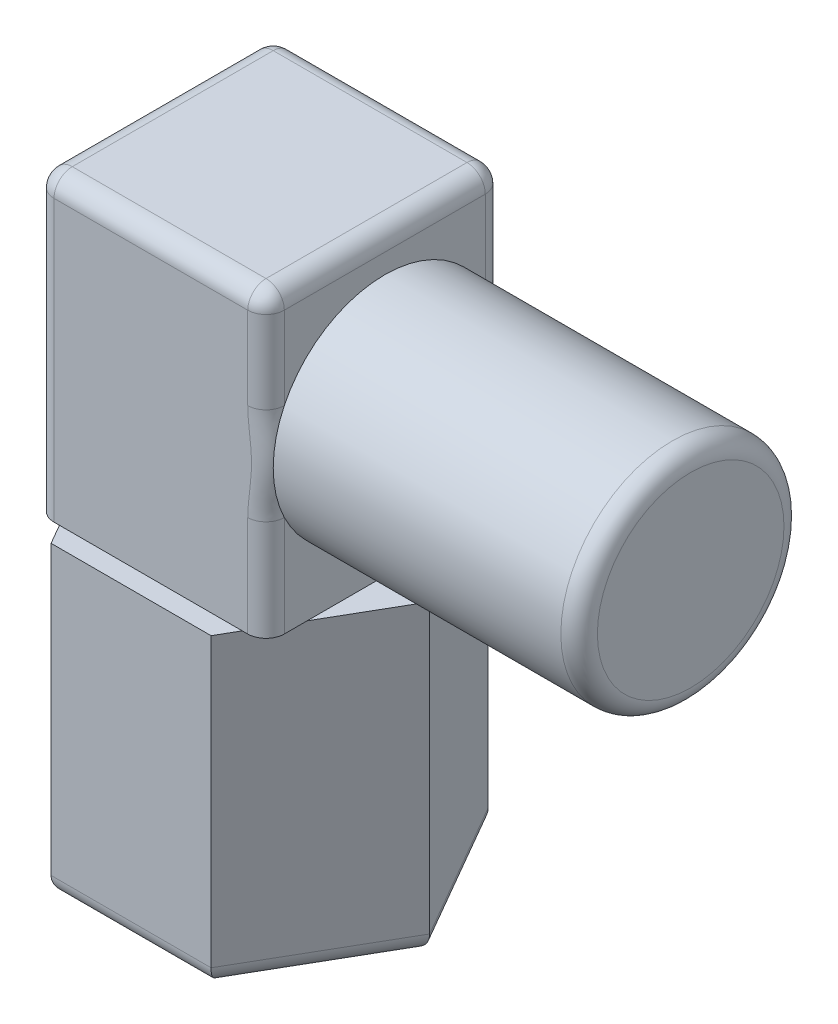
SolidWorks part; units mm, degrees
ref_plane "Front Plane" through (0, 0, 0) normal (0, 0, 1) x (1, 0, 0)
ref_plane "Top Plane" through (0, 0, 0) normal (0, 1, 0) x (1, 0, 0)
ref_plane "Right Plane" through (0, 0, 0) normal (1, 0, 0) x (0, 0, -1)
sketch "Sketch1" plane through (0, 0, 0) normal (0, 1, 0) x (1, 0, 0)
  line L1 (4.4456, 0) -> (2.2228, 3.85)
  line L2 (2.2228, 3.85) -> (-2.2228, 3.85)
  line L3 (-2.2228, 3.85) -> (-4.4456, 0)
  line L4 (-4.4456, 0) -> (-2.2228, -3.85)
  line L5 (-2.2228, -3.85) -> (2.2228, -3.85)
  line L6 (2.2228, -3.85) -> (4.4456, 0)
  circle A0 centre (0, 0) radius 4.4456 construction
  dimension "D1" = 7.7
extrude "Boss-Extrude1" add sketch "Sketch1" along normal blind 8.5
sketch "Sketch2" plane through (0, 8.5, 0) normal (0, 1, 0) x (1, 0, 0)
  line L0 (-3.2, 3.3) -> (3.2, -3.3) construction
  line L1 (-3.2, 3.3) -> (3.2, 3.3)
  line L2 (-3.2, 3.3) -> (-3.2, -3.3)
  line L3 (-3.2, -3.3) -> (3.2, -3.3)
  line L4 (3.2, 3.3) -> (3.2, -3.3)
  point P4 (0, 0)
  point P5 (0, 0)
  point P7 (0, 0)
  dimension "D1" = 6.4
  dimension "D2" = 6.6
extrude "Boss-Extrude2" add sketch "Sketch2" along normal blind 8.3
sketch "Sketch3" plane through (3.2, 0, 0) normal (1, 0, 0) x (0, 0, -1)
  line L0 (-3.3, 16.8) -> (3.3, 8.5) construction
  circle A0 centre (0, 12.65) radius 3.1
  point P6 (0, 12.65)
  dimension "D1" = 6.2
extrude "Boss-Extrude3" add sketch "Sketch3" along normal blind 8.5 contours A0
sketch "Sketch4" plane through (0, 0, 0) normal (0, -1, 0) x (1, 0, 0)
  circle A0 centre (0, 0) radius 3.1
  dimension "D1" = 6.2
extrude "Cut-Extrude1" cut sketch "Sketch4" against normal up to surface (8.5 mm away) contours A0 up to face at (2.9801, 8.5, 2.9191)
fillet "Fillet1" radius 0.508 15 edges at (11.7, 12.65, -3.1) (-3.3342, 0, 1.925) (-3.3342, 0, -1.925) (0, 0, -3.85) (3.3342, 0, -1.925) (3.3342, 0, 1.925) (0, 0, 3.85) (3.2, 12.65, 3.3) (3.2, 12.65, -3.3) (3.2, 16.8, 0) (0, 16.8, -3.3) (-3.2, 12.65, -3.3) (-3.2, 16.8, 0) (0, 16.8, 3.3) (-3.2, 12.65, 3.3)
